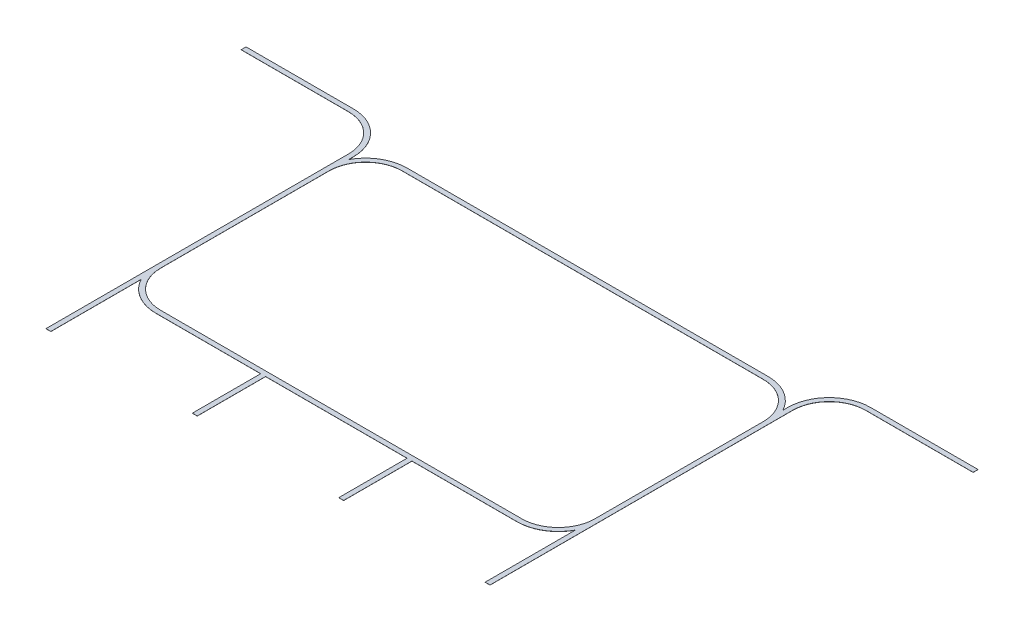
SolidWorks part; units mm, degrees
ref_plane "Plan de face" through (0, 0, 0) normal (0, 0, 1) x (1, 0, 0)
ref_plane "Plan de dessus" through (0, 0, 0) normal (0, 1, 0) x (1, 0, 0)
ref_plane "Plan de droite" through (0, 0, 0) normal (1, 0, 0) x (0, 0, -1)
sketch "Esquisse1" plane through (0, 0, 0) normal (0, 1, 0) x (1, 0, 0)
  line L0 (0, 0) -> (0, -1910.2704) construction
  line L1 (-740, 0) -> (740, 0)
  line L2 (-740, 20) -> (740, 20)
  line L3 (890, -150) -> (890, -840)
  line L4 (910, -1290) -> (910, -50)
  line L5 (890, -50) -> (890, -70)
  line L6 (1060, 100) -> (1500, 100)
  line L7 (1060, 120) -> (1500, 120)
  line L8 (1500, 120) -> (1500, 100)
  line L9 (910, -1290) -> (890, -1290)
  line L10 (890, -1290) -> (890, -920)
  line L11 (740, -990) -> (-740, -990)
  line L12 (310, -1010) -> (740, -1010)
  line L13 (-290, -1010) -> (290, -1010)
  line L14 (290, -1010) -> (290, -1290)
  line L15 (290, -1290) -> (310, -1290)
  line L16 (310, -1290) -> (310, -1010)
  line L17 (-310, -1290) -> (-310, -1010)
  line L18 (-290, -1290) -> (-310, -1290)
  line L19 (-290, -1010) -> (-290, -1290)
  line L20 (-310, -1010) -> (-740, -1010)
  line L21 (-890, -1290) -> (-890, -920)
  line L22 (-910, -1290) -> (-890, -1290)
  line L23 (-1500, 120) -> (-1500, 100)
  line L24 (-1060, 120) -> (-1500, 120)
  line L25 (-1060, 100) -> (-1500, 100)
  line L26 (-890, -50) -> (-890, -70)
  line L27 (-910, -1290) -> (-910, -50)
  line L28 (-890, -150) -> (-890, -840)
  arc A0 (740, 20) -> (890, -70) centre (740, -150) cw
  arc A1 (740, 0) -> (890, -150) centre (740, -150) cw
  arc A2 (910, -50) -> (1060, 100) centre (1060, -50) cw
  arc A3 (890, -50) -> (1060, 120) centre (1060, -50) cw
  arc A4 (890, -840) -> (740, -990) centre (740, -840) cw
  arc A5 (740, -1010) -> (890, -920) centre (740, -840) ccw
  arc A6 (-740, -1010) -> (-890, -920) centre (-740, -840) cw
  arc A7 (-890, -840) -> (-740, -990) centre (-740, -840) ccw
  arc A8 (-890, -50) -> (-1060, 120) centre (-1060, -50) ccw
  arc A9 (-910, -50) -> (-1060, 100) centre (-1060, -50) ccw
  arc A10 (-740, 0) -> (-890, -150) centre (-740, -150) ccw
  arc A11 (-740, 20) -> (-890, -70) centre (-740, -150) ccw
  point P8 (0, -990)
  point P48 (0, -1010)
  point P52 (0, 20)
  dimension "D2" = 150
  dimension "D4" = 590
  dimension "D5" = 150
  dimension "D9" = 150
  dimension "D1" = 20
  dimension "D3" = 20
  dimension "D6" = 1500
  dimension "D7" = 1410
  dimension "D8" = 100
  dimension "D10" = 20
  dimension "D11" = 300
  dimension "D12" = 20
  dimension "D13" = 1210
extrude "Extrusion1" add sketch "Esquisse1" along normal blind 0.5
